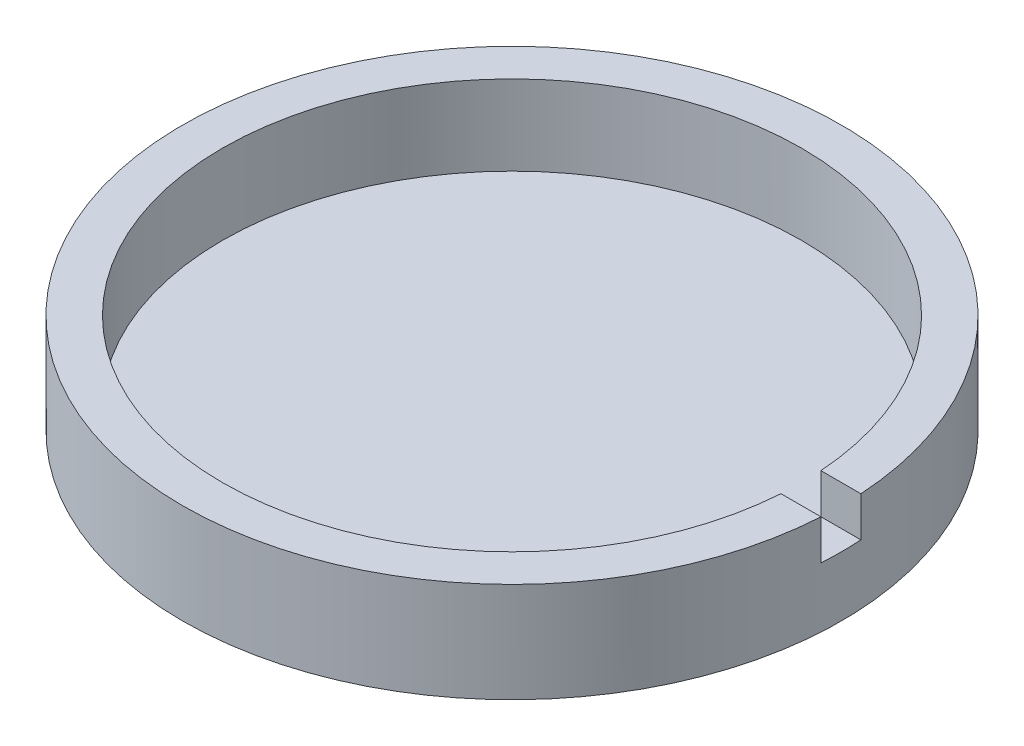
SolidWorks part; units mm, degrees
ref_plane "Спереди" through (0, 0, 0) normal (0, 0, 1) x (1, 0, 0)
ref_plane "Сверху" through (0, 0, 0) normal (0, 1, 0) x (1, 0, 0)
ref_plane "Справа" through (0, 0, 0) normal (1, 0, 0) x (0, 0, -1)
sketch "Эскиз1" plane through (0, 0, 0) normal (1, 0, 0) x (0, 0, -1)
  line L0 (0, 0) -> (16.5, 0)
  line L1 (16.5, 0) -> (16.5, 5)
  line L2 (16.5, 5) -> (14.5, 5)
  line L3 (14.5, 5) -> (14.5, 1)
  line L4 (14.5, 1) -> (0, 1)
  line L5 (0, 1) -> (0, 0)
  dimension "D1" = 14.5
  dimension "D2" = 2
  dimension "D3" = 1
  dimension "D4" = 5
revolve "Повернуть1" add sketch "Эскиз1" angle 360 about L5
sketch "Эскиз2" plane through (0, 5, 0) normal (0, 1, 0) x (1, 0, 0)
  line L0 (0, 0) -> (14.4655, 0) construction
  line L1 (14.4655, 1) -> (16.5, 1)
  line L2 (14.4655, 1) -> (14.4655, -1)
  line L3 (14.4655, -1) -> (16.5, -1)
  line L4 (16.5, 1) -> (16.5, -1)
  circle A0 centre (0, 0) radius 14.5 construction
  circle A1 centre (0, 0) radius 16.5 construction
  dimension "D1" = 2
extrude "Вырез-Вытянуть1" cut sketch "Эскиз2" against normal blind 2
